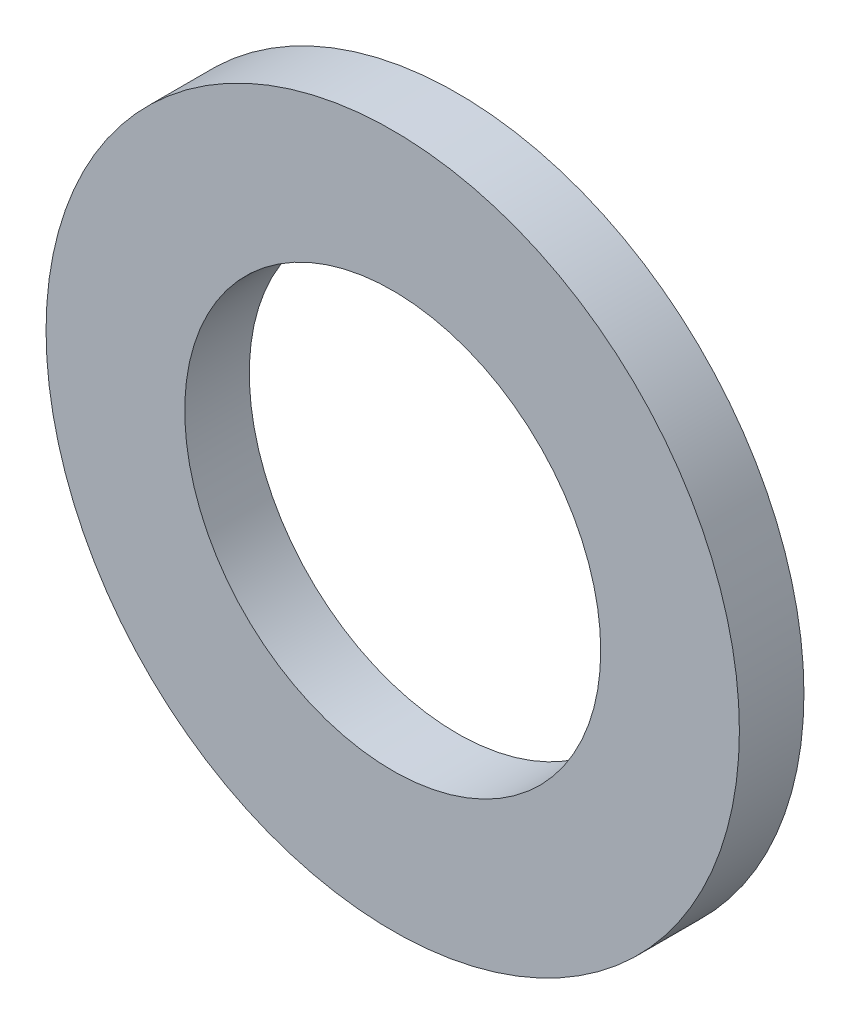
SolidWorks part; units mm, degrees
ref_plane "Front Plane" through (0, 0, 0) normal (0, 0, 1) x (1, 0, 0)
ref_plane "Top Plane" through (0, 0, 0) normal (0, 1, 0) x (1, 0, 0)
ref_plane "Right Plane" through (0, 0, 0) normal (1, 0, 0) x (0, 0, -1)
sketch "Sketch1" plane through (0, 0, 0) normal (0, 0, 1) x (1, 0, 0)
  circle A0 centre (0, 0) radius 12.7
  circle A1 centre (0, 0) radius 7.62
extrude "Boss-Extrude1" add sketch "Sketch1" along normal blind 2.3647
